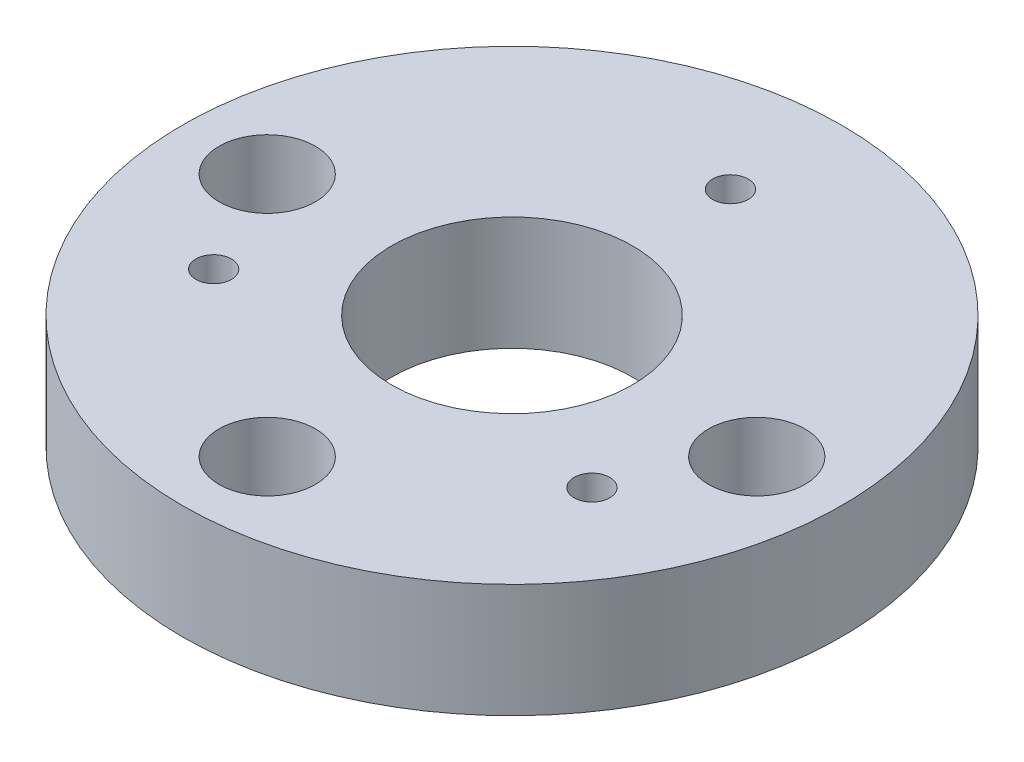
SolidWorks part; units mm, degrees
ref_plane "Front" through (0, 0, 0) normal (0, 0, 1) x (1, 0, 0)
ref_plane "Top" through (0, 0, 0) normal (0, 1, 0) x (1, 0, 0)
ref_plane "Right" through (0, 0, 0) normal (1, 0, 0) x (0, 0, -1)
sketch "Sketch1" plane through (0, 0, 0) normal (0, 1, 0) x (1, 0, 0)
  circle A0 centre (0, 0) radius 27.7876
  circle A1 centre (0, 0) radius 10.16
  dimension "D1" = 20.32
  dimension "D2" = 55.5752
extrude "Ring" add sketch "Sketch1" along normal blind 9.5885
sketch "Sketch2" plane through (0, 9.5885, 0) normal (0, 1, 0) x (1, 0, 0)
  circle A0 centre (0, 18.415) radius 1.5
  circle A1 centre (15.9479, -9.2075) radius 1.5
  circle A2 centre (-15.9479, -9.2075) radius 1.5
  point P8 (0, 0)
  dimension "D3" = 3
  dimension "D2" = 18.415
  dimension "D1" = 3
extrude "Robot Side1 - Holes" cut sketch "Sketch2" against normal through all
chamfer "Robot Side - Chamfer" distance 2.4 angle 45 3 edges at (-15.9479, 0, 10.7075) (15.9479, 0, 10.7075) (0, 0, -16.915)
sketch "Sketch3" plane through (0, 9.5885, 0) normal (0, 1, 0) x (1, 0, 0)
  circle A0 centre (20.6375, 0) radius 1.8387
  circle A1 centre (0, -20.6375) radius 1.8387
  circle A2 centre (-20.6375, 0) radius 1.8387
  point P2 (12.2643, 12.2643)
  point P3 (31.7912, 0)
  point P4 (0, 0)
  point P11 (0, 0)
  point P12 (0, 0)
  point P14 (0, 0)
  point P15 (0, 0)
  point P16 (0, 0)
  dimension "D2" = 20.6375
extrude "Tool Side - Holes" cut sketch "Sketch3" against normal through all
sketch "Sketch4" plane through (0, 9.5885, 0) normal (0, 1, 0) x (1, 0, 0)
  circle A0 centre (-20.6375, 0) radius 4.064
  circle A1 centre (0, -20.6375) radius 4.064
  circle A2 centre (20.6375, 0) radius 4.064
  dimension "D1" = 8.128
  dimension "D2" = 8.128
  dimension "D3" = 8.128
extrude "Tool Side - Inset" cut sketch "Sketch4" against normal blind 6
equation "\"D2@Sketch4\"=\"D1@Sketch4\""
equation "\"D3@Sketch4\"=\"D1@Sketch4\""
